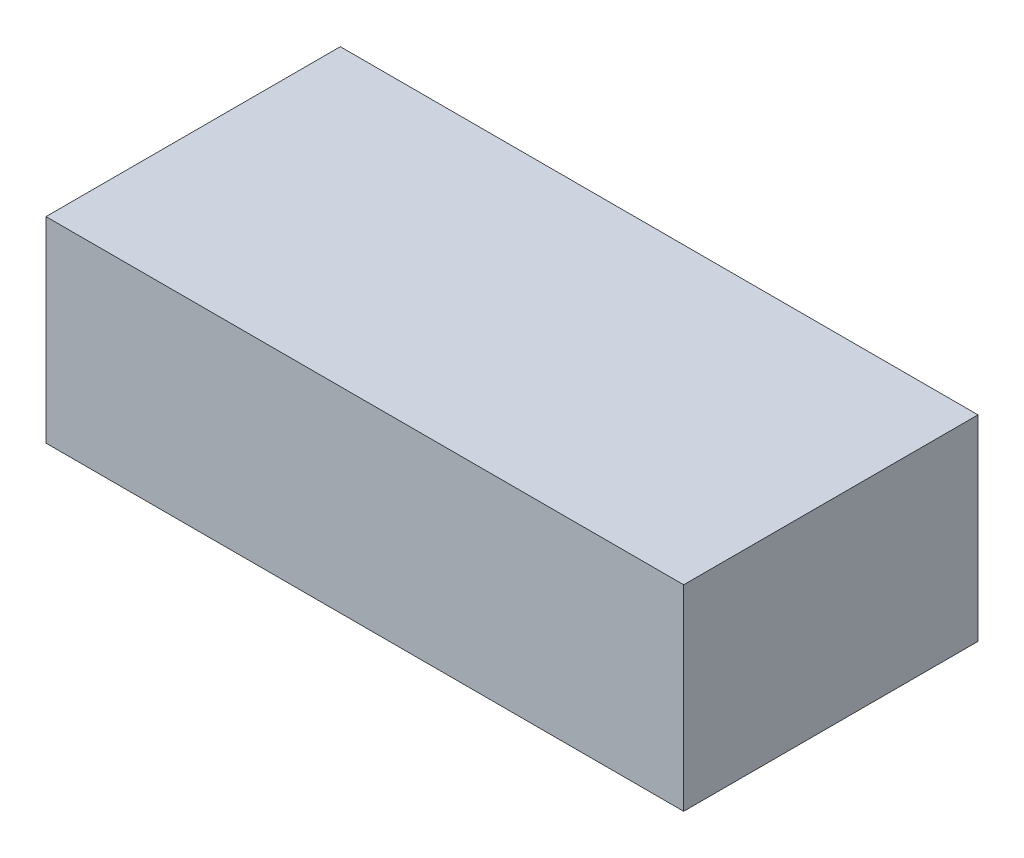
SolidWorks part; units mm, degrees
material "Cast Alloy Steel"
ref_plane "Front Plane" through (0, 0, 0) normal (0, 0, 1) x (1, 0, 0)
ref_plane "Top Plane" through (0, 0, 0) normal (0, 1, 0) x (1, 0, 0)
ref_plane "Right Plane" through (0, 0, 0) normal (1, 0, 0) x (0, 0, -1)
sketch "Sketch1" plane through (0, 0, 0) normal (0, 1, 0) x (1, 0, 0)
  line L1 (8.255, -3.81) -> (-8.255, -3.81)
  line L2 (8.255, -3.81) -> (8.255, 3.81)
  line L3 (8.255, 3.81) -> (-8.255, 3.81)
  line L4 (-8.255, -3.81) -> (-8.255, 3.81)
  line L5 (8.255, -3.81) -> (-8.255, 3.81) construction
  line L6 (8.255, 3.81) -> (-8.255, -3.81) construction
  point P0 (0, 0)
extrude "Extrude1" add sketch "Sketch1" along normal blind 5.08
